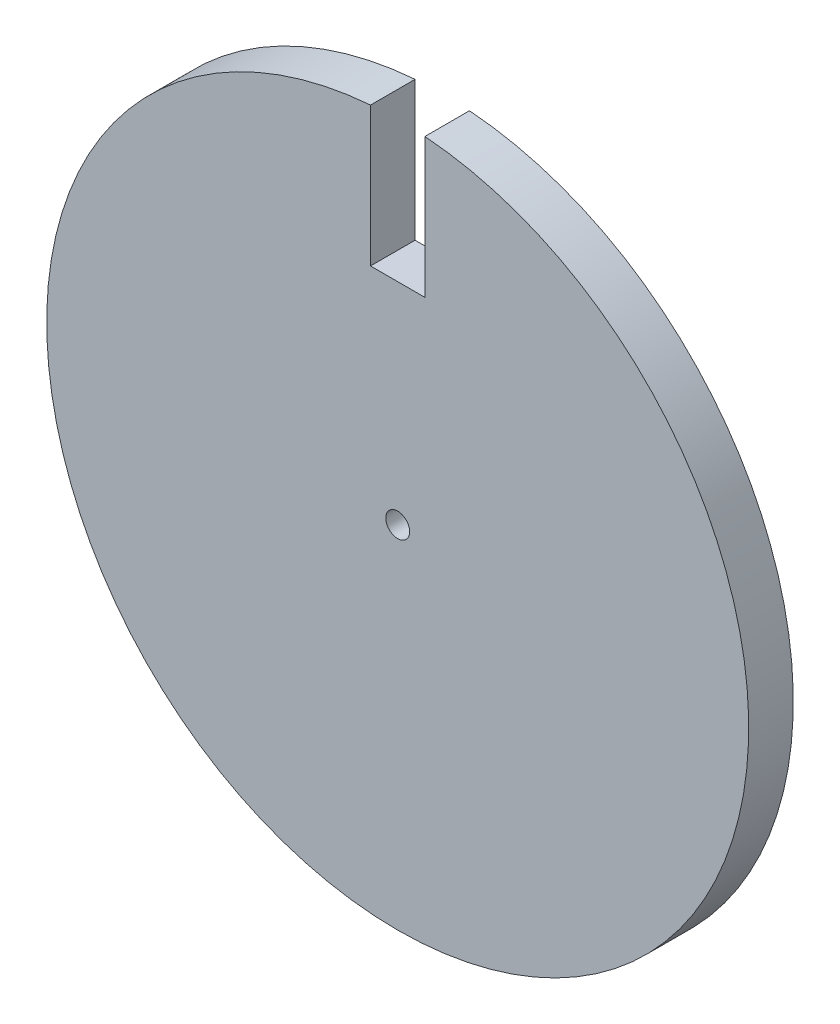
SolidWorks part; units mm, degrees
ref_plane "Front Plane" through (0, 0, 0) normal (0, 0, 1) x (1, 0, 0)
ref_plane "Top Plane" through (0, 0, 0) normal (0, 1, 0) x (1, 0, 0)
ref_plane "Right Plane" through (0, 0, 0) normal (1, 0, 0) x (0, 0, -1)
sketch "Sketch1" plane through (0, 0, 0) normal (0, 0, 1) x (1, 0, 0)
  circle A0 centre (0, 0) radius 25
  circle A1 centre (0, 0) radius 0.85
  dimension "D1" = 1.7
  dimension "D2" = 50
extrude "Boss-Extrude1" add sketch "Sketch1" along normal mid plane 3.175
sketch "Sketch2" plane through (0, 0, -1.5875) normal (0, 0, -1) x (-1, 0, 0)
  line L0 (0, 0) -> (0, 25) construction
  line L1 (1.937, 34.0448) -> (-1.937, 34.0448)
  line L2 (-1.937, 34.0448) -> (-1.937, 15)
  line L3 (-1.937, 15) -> (1.937, 15)
  line L4 (1.937, 15) -> (1.937, 34.0448)
  circle A0 centre (0, 0) radius 25 construction
  point P9 (0, 34.0448)
  dimension "D1" = 15
extrude "Cut-Extrude1" cut sketch "Sketch2" against normal up to body separate body
